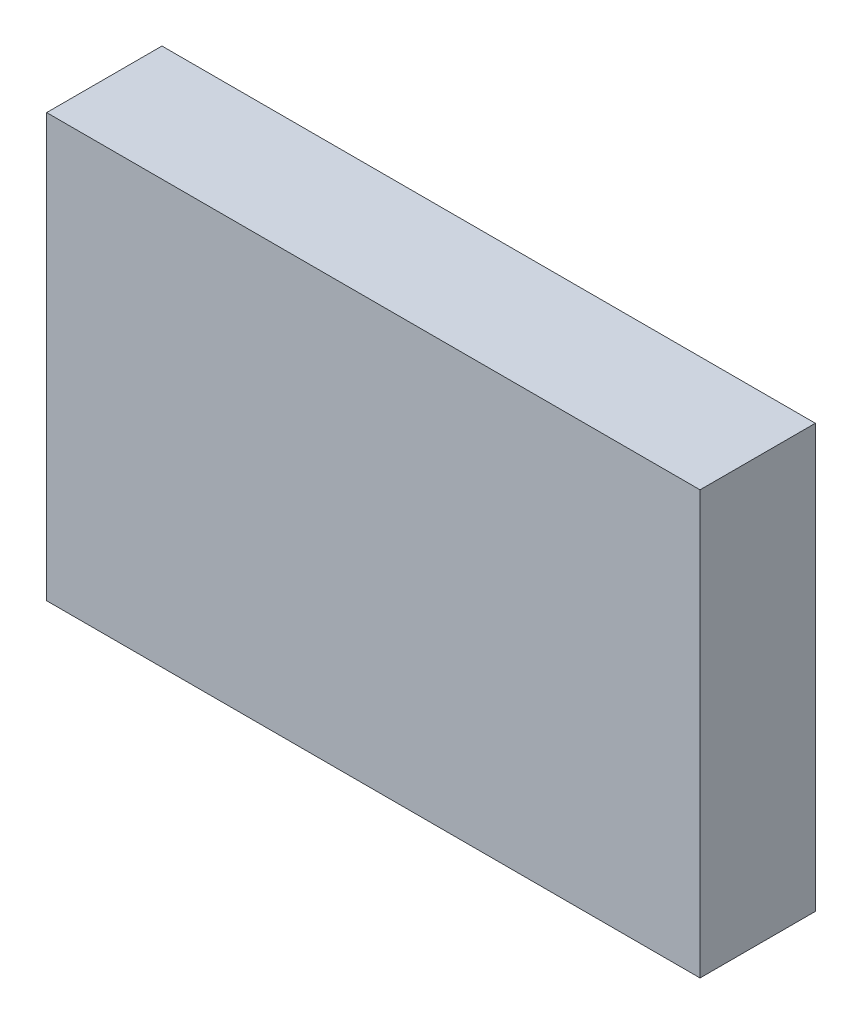
SolidWorks part; units mm, degrees
ref_plane "Front Plane" through (0, 0, 0) normal (0, 0, 1) x (1, 0, 0)
ref_plane "Top Plane" through (0, 0, 0) normal (0, 1, 0) x (1, 0, 0)
ref_plane "Right Plane" through (0, 0, 0) normal (1, 0, 0) x (0, 0, -1)
sketch "Sketch1" plane through (0, 0, 0) normal (0, 0, 1) x (1, 0, 0)
  line L1 (-42.5, -27.5) -> (42.5, -27.5)
  line L2 (-42.5, -27.5) -> (-42.5, 27.5)
  line L3 (-42.5, 27.5) -> (42.5, 27.5)
  line L4 (42.5, -27.5) -> (42.5, 27.5)
  line L5 (-42.5, -27.5) -> (42.5, 27.5) construction
  line L6 (-42.5, 27.5) -> (42.5, -27.5) construction
  point P0 (0, 0)
  dimension "D1" = 85
  dimension "D2" = 55
extrude "Boss-Extrude1" add sketch "Sketch1" along normal blind 15 contours L4 L3 L2 L1
